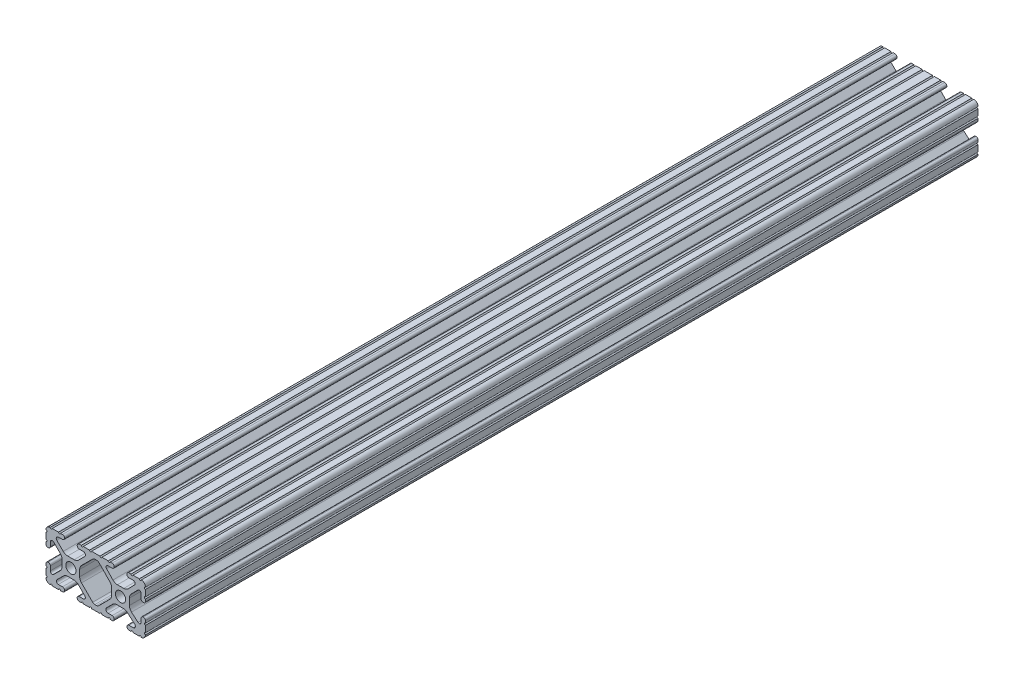
SolidWorks part; units mm, degrees
ref_plane "Front Plane" through (0, 0, 0) normal (0, 0, 1) x (1, 0, 0)
ref_plane "Top Plane" through (0, 0, 0) normal (0, 1, 0) x (1, 0, 0)
ref_plane "Right Plane" through (0, 0, 0) normal (1, 0, 0) x (0, 0, -1)
sketch "Sketch1" plane through (0, 0, 0) normal (0, 0, 1) x (1, 0, 0)
  line L0 (-7.2595, -3.8694) -> (-1.5457, -9.5728)
  line L1 (-8.1915, 1.6223) -> (-8.1915, -1.6223)
  line L2 (-1.504, 9.5765) -> (-7.252, 3.8768)
  line L3 (0.5515, 10.033) -> (-0.3952, 10.033)
  line L4 (7.2829, 3.8459) -> (1.6756, 9.5611)
  line L5 (8.1915, -1.6223) -> (8.1915, 1.6223)
  line L6 (1.5457, -9.5728) -> (7.2595, -3.8694)
  line L7 (-0.4332, -10.033) -> (0.4332, -10.033)
  line L8 (18.0171, 12.7) -> (16.9875, 12.7)
  line L9 (15.9385, 11.651) -> (15.9385, 11.5392)
  line L10 (16.9875, 10.4902) -> (19.1164, 10.4902)
  line L11 (19.8441, 8.7652) -> (16.619, 5.4551)
  line L12 (14.3449, 4.4958) -> (11.0833, 4.4958)
  line L13 (8.817, 5.4472) -> (5.5642, 8.7627)
  line L14 (6.2894, 10.4902) -> (8.4125, 10.4902)
  line L15 (9.4615, 11.5392) -> (9.4615, 11.651)
  line L16 (8.4125, 12.7) -> (7.3829, 12.7)
  line L17 (6.3669, 12.7) -> (3.1496, 12.7)
  line L18 (2.1336, 12.7) -> (-2.1336, 12.7)
  line L19 (-3.1496, 12.7) -> (-6.3669, 12.7)
  line L20 (-7.3829, 12.7) -> (-8.4125, 12.7)
  line L21 (-9.4615, 11.651) -> (-9.4615, 11.5392)
  line L22 (-8.4125, 10.4902) -> (-6.2836, 10.4902)
  line L23 (-5.5326, 8.6661) -> (-8.81, 5.4163)
  line L24 (-11.0455, 4.4958) -> (-14.3545, 4.4958)
  line L25 (-16.59, 5.4163) -> (-19.8674, 8.6661)
  line L26 (-19.1164, 10.4902) -> (-16.9875, 10.4902)
  line L27 (-15.9385, 11.5392) -> (-15.9385, 11.651)
  line L28 (-16.9875, 12.7) -> (-18.0171, 12.7)
  line L29 (-19.0331, 12.7) -> (-22.2504, 12.7)
  line L30 (-25.4, 9.5504) -> (-25.4, 6.3331)
  line L31 (-25.4, 5.3171) -> (-25.4, 4.2375)
  line L32 (-24.401, 3.2385) -> (-24.2392, 3.2385)
  line L33 (-23.1902, 4.2875) -> (-23.1902, 6.3347)
  line L34 (-21.434, 7.0665) -> (-18.148, 3.8082)
  line L35 (-17.2085, 1.5536) -> (-17.2085, -1.6952)
  line L36 (-18.1405, -3.9423) -> (-21.4316, -7.2274)
  line L37 (-23.1902, -6.498) -> (-23.1902, -4.2875)
  line L38 (-24.2392, -3.2385) -> (-24.351, -3.2385)
  line L39 (-25.4, -4.2875) -> (-25.4, -5.3171)
  line L40 (-25.4, -6.3331) -> (-25.4, -9.5504)
  line L41 (-22.2504, -12.7) -> (-19.0331, -12.7)
  line L42 (-18.0171, -12.7) -> (-16.9875, -12.7)
  line L43 (-15.9384, -11.651) -> (-15.9384, -11.5392)
  line L44 (-16.9875, -10.4902) -> (-19.1164, -10.4902)
  line L45 (-19.8341, -8.7551) -> (-16.4966, -5.4237)
  line L46 (-14.2536, -4.4958) -> (-11.1464, -4.4958)
  line L47 (-8.9034, -5.4237) -> (-5.5659, -8.7551)
  line L48 (-6.2836, -10.4902) -> (-8.4125, -10.4902)
  line L49 (-9.4616, -11.5392) -> (-9.4616, -11.651)
  line L50 (-8.4125, -12.7) -> (-7.3829, -12.7)
  line L51 (-6.3669, -12.7) -> (-3.1496, -12.7)
  line L52 (-2.1336, -12.7) -> (2.1336, -12.7)
  line L53 (3.1496, -12.7) -> (6.3669, -12.7)
  line L54 (7.3829, -12.7) -> (8.4125, -12.7)
  line L55 (9.4616, -11.651) -> (9.4616, -11.5392)
  line L56 (8.4125, -10.4902) -> (6.2894, -10.4902)
  line L57 (5.4807, -8.5353) -> (8.5979, -5.4237)
  line L58 (10.8409, -4.4958) -> (14.1026, -4.4958)
  line L59 (16.1879, -5.2766) -> (19.8682, -8.4822)
  line L60 (19.1164, -10.4902) -> (16.9875, -10.4902)
  line L61 (15.9384, -11.5392) -> (15.9384, -11.651)
  line L62 (16.9875, -12.7) -> (18.0171, -12.7)
  line L63 (19.0331, -12.7) -> (22.2504, -12.7)
  line L64 (25.4, -9.5504) -> (25.4, -6.3331)
  line L65 (25.4, -5.3171) -> (25.4, -4.2375)
  line L66 (24.401, -3.2385) -> (24.1892, -3.2385)
  line L67 (23.1902, -4.2375) -> (23.1902, -6.1559)
  line L68 (21.584, -6.8869) -> (18.2982, -4.025)
  line L69 (17.2085, -1.6308) -> (17.2085, 1.6308)
  line L70 (18.1094, 3.8465) -> (21.5263, 7.3534)
  line L71 (23.1902, 6.6769) -> (23.1902, 4.2375)
  line L72 (24.1892, 3.2385) -> (24.401, 3.2385)
  line L73 (25.4, 4.2375) -> (25.4, 5.3171)
  line L74 (25.4, 6.3332) -> (25.4, 9.5504)
  line L75 (22.2504, 12.7) -> (19.0331, 12.7)
  circle A0 centre (-12.7, 0) radius 2.6035
  circle A1 centre (12.7, 0) radius 2.6035
  arc A2 (-1.5457, -9.5728) -> (-0.4332, -10.033) centre (-0.4332, -8.4582) ccw
  arc A3 (-8.1915, -1.6223) -> (-7.2595, -3.8694) centre (-5.0165, -1.6223) ccw
  arc A4 (-7.252, 3.8768) -> (-8.1915, 1.6223) centre (-5.0165, 1.6223) ccw
  arc A5 (-0.3952, 10.033) -> (-1.504, 9.5765) centre (-0.3952, 8.4582) ccw
  arc A6 (1.6756, 9.5611) -> (0.5515, 10.033) centre (0.5515, 8.4582) ccw
  arc A7 (8.1915, 1.6223) -> (7.2829, 3.8459) centre (5.0165, 1.6223) ccw
  arc A8 (7.2595, -3.8694) -> (8.1915, -1.6223) centre (5.0165, -1.6223) ccw
  arc A9 (0.4332, -10.033) -> (1.5457, -9.5728) centre (0.4332, -8.4582) ccw
  arc A10 (18.0171, 12.7) -> (19.0331, 12.7) centre (18.5251, 12.7) ccw
  arc A11 (16.9875, 12.7) -> (15.9385, 11.651) centre (16.9875, 11.651) ccw
  arc A12 (15.9385, 11.5392) -> (16.9875, 10.4902) centre (16.9875, 11.5392) ccw
  arc A13 (19.8441, 8.7652) -> (19.1164, 10.4902) centre (19.1164, 9.4742) ccw
  arc A14 (14.3449, 4.4958) -> (16.619, 5.4551) centre (14.3449, 7.6708) ccw
  arc A15 (8.817, 5.4472) -> (11.0833, 4.4958) centre (11.0833, 7.6708) ccw
  arc A16 (6.2894, 10.4902) -> (5.5642, 8.7627) centre (6.2894, 9.4742) ccw
  arc A17 (8.4125, 10.4902) -> (9.4615, 11.5392) centre (8.4125, 11.5392) ccw
  arc A18 (9.4615, 11.651) -> (8.4125, 12.7) centre (8.4125, 11.651) ccw
  arc A19 (6.3669, 12.7) -> (7.3829, 12.7) centre (6.8749, 12.7) ccw
  arc A20 (2.1336, 12.7) -> (3.1496, 12.7) centre (2.6416, 12.7) ccw
  arc A21 (-3.1496, 12.7) -> (-2.1336, 12.7) centre (-2.6416, 12.7) ccw
  arc A22 (-7.3829, 12.7) -> (-6.3669, 12.7) centre (-6.8749, 12.7) ccw
  arc A23 (-8.4125, 12.7) -> (-9.4615, 11.651) centre (-8.4125, 11.651) ccw
  arc A24 (-9.4615, 11.5392) -> (-8.4125, 10.4902) centre (-8.4125, 11.5392) ccw
  arc A25 (-5.5326, 8.6661) -> (-6.2836, 10.4902) centre (-6.2836, 9.4235) ccw
  arc A26 (-11.0455, 4.4958) -> (-8.81, 5.4163) centre (-11.0455, 7.6708) ccw
  arc A27 (-16.59, 5.4163) -> (-14.3545, 4.4958) centre (-14.3545, 7.6708) ccw
  arc A28 (-19.1164, 10.4902) -> (-19.8674, 8.6661) centre (-19.1164, 9.4235) ccw
  arc A29 (-16.9875, 10.4902) -> (-15.9385, 11.5392) centre (-16.9875, 11.5392) ccw
  arc A30 (-15.9385, 11.651) -> (-16.9875, 12.7) centre (-16.9875, 11.651) ccw
  arc A31 (-19.0331, 12.7) -> (-18.0171, 12.7) centre (-18.5251, 12.7) ccw
  arc A32 (-23.2664, 12.6998) -> (-22.2504, 12.7) centre (-22.7584, 12.7) ccw
  arc A33 (-23.2664, 12.6998) -> (-25.3998, 10.5664) centre (-23.2918, 10.5918) ccw
  arc A34 (-25.4, 9.5504) -> (-25.3998, 10.5664) centre (-25.4, 10.0584) ccw
  arc A35 (-25.4, 5.3171) -> (-25.4, 6.3331) centre (-25.4, 5.8251) ccw
  arc A36 (-25.4, 4.2375) -> (-24.401, 3.2385) centre (-24.401, 4.2375) ccw
  arc A37 (-24.2392, 3.2385) -> (-23.1902, 4.2875) centre (-24.2392, 4.2875) ccw
  arc A38 (-21.434, 7.0665) -> (-23.1902, 6.3347) centre (-22.1596, 6.3347) ccw
  arc A39 (-17.2085, 1.5536) -> (-18.148, 3.8082) centre (-20.3835, 1.5536) ccw
  arc A40 (-18.1405, -3.9423) -> (-17.2085, -1.6952) centre (-20.3835, -1.6952) ccw
  arc A41 (-23.1902, -6.498) -> (-21.4316, -7.2274) centre (-22.1596, -6.498) ccw
  arc A42 (-23.1902, -4.2875) -> (-24.2392, -3.2385) centre (-24.2392, -4.2875) ccw
  arc A43 (-24.351, -3.2385) -> (-25.4, -4.2875) centre (-24.351, -4.2875) ccw
  arc A44 (-25.4, -6.3331) -> (-25.4, -5.3171) centre (-25.4, -5.8251) ccw
  arc A45 (-25.3998, -10.5664) -> (-25.4, -9.5504) centre (-25.4, -10.0584) ccw
  arc A46 (-25.3998, -10.5664) -> (-23.2664, -12.6998) centre (-23.2918, -10.5918) ccw
  arc A47 (-22.2504, -12.7) -> (-23.2664, -12.6998) centre (-22.7584, -12.7) ccw
  arc A48 (-18.0171, -12.7) -> (-19.0331, -12.7) centre (-18.5251, -12.7) ccw
  arc A49 (-16.9875, -12.7) -> (-15.9384, -11.651) centre (-16.9875, -11.651) ccw
  arc A50 (-15.9384, -11.5392) -> (-16.9875, -10.4902) centre (-16.9875, -11.5392) ccw
  arc A51 (-19.8341, -8.7551) -> (-19.1164, -10.4902) centre (-19.1164, -9.4742) ccw
  arc A52 (-14.2536, -4.4958) -> (-16.4966, -5.4237) centre (-14.2536, -7.6708) ccw
  arc A53 (-8.9034, -5.4237) -> (-11.1464, -4.4958) centre (-11.1464, -7.6708) ccw
  arc A54 (-6.2836, -10.4902) -> (-5.5659, -8.7551) centre (-6.2836, -9.4742) ccw
  arc A55 (-8.4125, -10.4902) -> (-9.4616, -11.5392) centre (-8.4125, -11.5392) ccw
  arc A56 (-9.4616, -11.651) -> (-8.4125, -12.7) centre (-8.4125, -11.651) ccw
  arc A57 (-6.3669, -12.7) -> (-7.3829, -12.7) centre (-6.8749, -12.7) ccw
  arc A58 (-2.1336, -12.7) -> (-3.1496, -12.7) centre (-2.6416, -12.7) ccw
  arc A59 (3.1496, -12.7) -> (2.1336, -12.7) centre (2.6416, -12.7) ccw
  arc A60 (7.3829, -12.7) -> (6.3669, -12.7) centre (6.8749, -12.7) ccw
  arc A61 (8.4125, -12.7) -> (9.4616, -11.651) centre (8.4125, -11.651) ccw
  arc A62 (9.4616, -11.5392) -> (8.4125, -10.4902) centre (8.4125, -11.5392) ccw
  arc A63 (5.4807, -8.5353) -> (6.2894, -10.4902) centre (6.2894, -9.3455) ccw
  arc A64 (10.8409, -4.4958) -> (8.5979, -5.4237) centre (10.8409, -7.6708) ccw
  arc A65 (16.1879, -5.2766) -> (14.1026, -4.4958) centre (14.1026, -7.6708) ccw
  arc A66 (19.1164, -10.4902) -> (19.8682, -8.4822) centre (19.1164, -9.3455) ccw
  arc A67 (16.9875, -10.4902) -> (15.9384, -11.5392) centre (16.9875, -11.5392) ccw
  arc A68 (15.9384, -11.651) -> (16.9875, -12.7) centre (16.9875, -11.651) ccw
  arc A69 (19.0331, -12.7) -> (18.0171, -12.7) centre (18.5251, -12.7) ccw
  arc A70 (23.2664, -12.6998) -> (22.2504, -12.7) centre (22.7584, -12.7) ccw
  arc A71 (23.2664, -12.6998) -> (25.3998, -10.5664) centre (23.2918, -10.5918) ccw
  arc A72 (25.4, -9.5504) -> (25.3998, -10.5664) centre (25.4, -10.0584) ccw
  arc A73 (25.4, -5.3171) -> (25.4, -6.3331) centre (25.4, -5.8251) ccw
  arc A74 (25.4, -4.2375) -> (24.401, -3.2385) centre (24.401, -4.2375) ccw
  arc A75 (24.1892, -3.2385) -> (23.1902, -4.2375) centre (24.1892, -4.2375) ccw
  arc A76 (21.584, -6.8869) -> (23.1902, -6.1559) centre (22.2207, -6.1559) ccw
  arc A77 (17.2085, -1.6308) -> (18.2982, -4.025) centre (20.3835, -1.6308) ccw
  arc A78 (18.1094, 3.8465) -> (17.2085, 1.6308) centre (20.3835, 1.6308) ccw
  arc A79 (23.1902, 6.6769) -> (21.5263, 7.3534) centre (22.2207, 6.6769) ccw
  arc A80 (23.1902, 4.2375) -> (24.1892, 3.2385) centre (24.1892, 4.2375) ccw
  arc A81 (24.401, 3.2385) -> (25.4, 4.2375) centre (24.401, 4.2375) ccw
  arc A82 (25.4, 6.3332) -> (25.4, 5.3171) centre (25.4, 5.8251) ccw
  arc A83 (25.3998, 10.5664) -> (25.4, 9.5504) centre (25.4, 10.0584) ccw
  arc A84 (25.3998, 10.5664) -> (23.2664, 12.6998) centre (23.2918, 10.5918) ccw
  arc A85 (22.2504, 12.7) -> (23.2664, 12.6998) centre (22.7584, 12.7) ccw
  point P248 (0, 10.033)
extrude "Boss-Extrude1" add sketch "Sketch1" along normal mid plane 425.45
